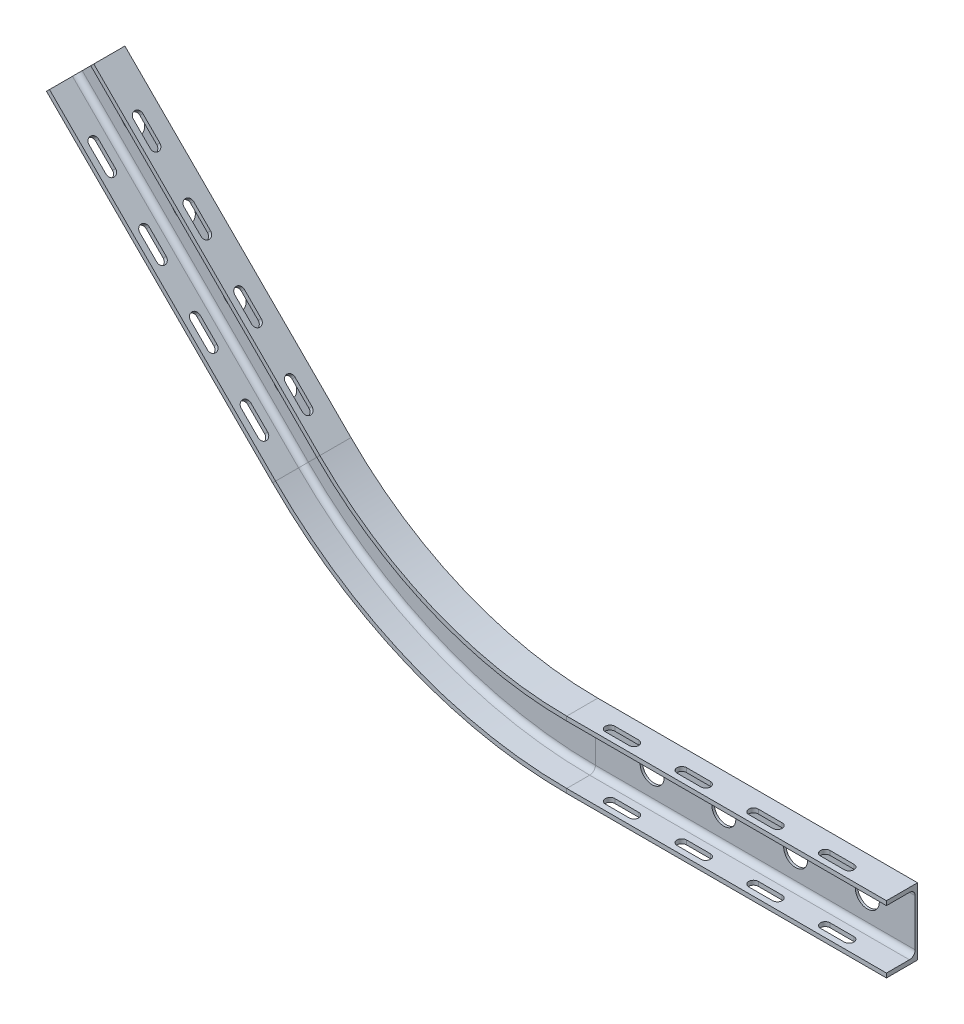
SolidWorks part; units mm, degrees
material "Acier S235JRG2 (E24 // 1.0038)"
ref_plane "Face" through (0, 0, 0) normal (0, 0, 1) x (1, 0, 0)
ref_plane "Dessus" through (0, 0, 0) normal (0, 1, 0) x (1, 0, 0)
ref_plane "Droite" through (0, 0, 0) normal (1, 0, 0) x (0, 0, -1)
sketch "Esquisse1" plane through (0, 0, 0) normal (0, 0, 1) x (1, 0, 0)
  line L0 (-707.1068, 707.1068) -> (-234.3146, 234.3146)
  line L1 (331.3708, 0) -> (1000, 0)
  arc A0 (-234.3146, 234.3146) -> (331.3708, 0) centre (331.3708, 800) ccw
  point P6 (0, 0)
  dimension "D3" = 800
  dimension "D1" = 45
  dimension "D2" = 1000
other "Upe UPE 140(1)"
ref_plane "Plan1" through (-707.1068, 707.1068, 0) normal (0.7071, -0.7071, 0) x (0.7071, 0.7071, 0)
sketch "Skizze1" plane through (-707.1068, 707.1068, 0) normal (0.7071, -0.7071, 0) x (0.7071, 0.7071, 0)
  line L0 (0, 0) -> (0, 65) construction
  line L1 (-70, 65) -> (-61, 65)
  line L2 (-70, 0) -> (70, 0)
  line L6 (70, 0) -> (70, 65)
  line L7 (-49, 5) -> (49, 5)
  line L9 (-61, 65) -> (-61, 17)
  line L10 (61, 65) -> (70, 65)
  line L12 (-70, 65) -> (-70, 0)
  line L15 (61, 17) -> (61, 65)
  arc A4 (-49, 5) -> (-61, 17) centre (-49, 17) cw
  arc A7 (49, 5) -> (61, 17) centre (49, 17) ccw
  point P1 (0, 0)
  point P2 (0, 65)
  point P3 (0, 0)
  dimension "D3" = 9
  dimension "D1" = 12
  dimension "D2" = 65
  dimension "D4" = 5
  dimension "D5" = 140
sketch "Esquisse3" plane through (49.4975, 49.4975, 0) normal (0.7071, 0.7071, 0) x (0, 0, -1)
  line L0 (-43, 900) -> (-43, 850) construction
  line L1 (-33, 900) -> (-33, 850)
  line L2 (-53, 900) -> (-53, 850)
  line L3 (-65, 331.3708) -> (-65, 1000) construction
  line L4 (0, 1000) -> (-65, 1000) construction
  line L5 (-43, 750) -> (-43, 700) construction
  line L6 (-33, 750) -> (-33, 700)
  line L7 (-53, 750) -> (-53, 700)
  line L8 (-43, 600) -> (-43, 550) construction
  line L9 (-33, 600) -> (-33, 550)
  line L10 (-53, 600) -> (-53, 550)
  line L11 (-43, 450) -> (-43, 400) construction
  line L12 (-33, 450) -> (-33, 400)
  line L13 (-53, 450) -> (-53, 400)
  arc A0 (-33, 900) -> (-53, 900) centre (-43, 900) ccw
  arc A1 (-53, 850) -> (-33, 850) centre (-43, 850) ccw
  arc A2 (-33, 750) -> (-53, 750) centre (-43, 750) ccw
  arc A3 (-53, 700) -> (-33, 700) centre (-43, 700) ccw
  arc A4 (-33, 600) -> (-53, 600) centre (-43, 600) ccw
  arc A5 (-53, 550) -> (-33, 550) centre (-43, 550) ccw
  arc A6 (-33, 450) -> (-53, 450) centre (-43, 450) ccw
  arc A7 (-53, 400) -> (-33, 400) centre (-43, 400) ccw
  point P2 (-43, 875)
  point P14 (-43, 725)
  point P21 (-43, 575)
  point P28 (-43, 425)
  dimension "D1" = 22
  dimension "D2" = 20
  dimension "D3" = 50
  dimension "D4" = 100
  dimension "D6" = 100
  dimension "D5" = 4
extrude "Enlèv. mat.-Extru.1" cut sketch "Esquisse3" against normal through all
sketch "Esquisse4" plane through (0, 70, 0) normal (0, 1, 0) x (1, 0, 0)
  line L0 (900, -43) -> (850, -43) construction
  line L1 (900, -53) -> (850, -53)
  line L2 (900, -33) -> (850, -33)
  line L3 (1000, -65) -> (331.3708, -65) construction
  line L4 (750, -43) -> (700, -43) construction
  line L5 (750, -53) -> (700, -53)
  line L6 (750, -33) -> (700, -33)
  line L7 (600, -43) -> (550, -43) construction
  line L8 (600, -53) -> (550, -53)
  line L9 (600, -33) -> (550, -33)
  line L10 (450, -43) -> (400, -43) construction
  line L11 (450, -53) -> (400, -53)
  line L12 (450, -33) -> (400, -33)
  arc A0 (900, -53) -> (900, -33) centre (900, -43) ccw
  arc A1 (850, -33) -> (850, -53) centre (850, -43) ccw
  arc A2 (750, -53) -> (750, -33) centre (750, -43) ccw
  arc A3 (700, -33) -> (700, -53) centre (700, -43) ccw
  arc A4 (600, -53) -> (600, -33) centre (600, -43) ccw
  arc A5 (550, -33) -> (550, -53) centre (550, -43) ccw
  arc A6 (450, -53) -> (450, -33) centre (450, -43) ccw
  arc A7 (400, -33) -> (400, -53) centre (400, -43) ccw
  point P2 (875, -43)
  point P13 (725, -43)
  point P20 (575, -43)
  point P27 (425, -43)
  dimension "D1" = 22
  dimension "D2" = 20
  dimension "D3" = 50
  dimension "D4" = 100
  dimension "D6" = 100
  dimension "D5" = 4
extrude "Enlèv. mat.-Extru.2" cut sketch "Esquisse4" against normal through all
sketch "Esquisse5" plane through (0, 0, 5) normal (0, 0, 1) x (1, 0, 0)
  line L0 (-707.1068, 707.1068) -> (-234.3146, 234.3146) construction
  line L1 (-672.4585, 741.755) -> (-741.755, 672.4585) construction
  line L2 (331.3708, 70) -> (-184.8171, 283.812) construction
  line L3 (0, 0) -> (73.2769, 176.906) construction
  circle A0 centre (-636.3961, 636.3961) radius 25
  circle A1 centre (-530.3301, 530.3301) radius 25
  circle A2 centre (-424.2641, 424.2641) radius 25
  circle A3 centre (-318.1981, 318.1981) radius 25
  circle A4 centre (900, 0) radius 25
  circle A5 centre (750, 0) radius 25
  circle A6 centre (600, 0) radius 25
  circle A7 centre (450, 0) radius 25
  dimension "D1" = 50
  dimension "D2" = 100
  dimension "D4" = 150
  dimension "D3" = 4
extrude "Enlèv. mat.-Extru.3" cut sketch "Esquisse5" against normal through all
